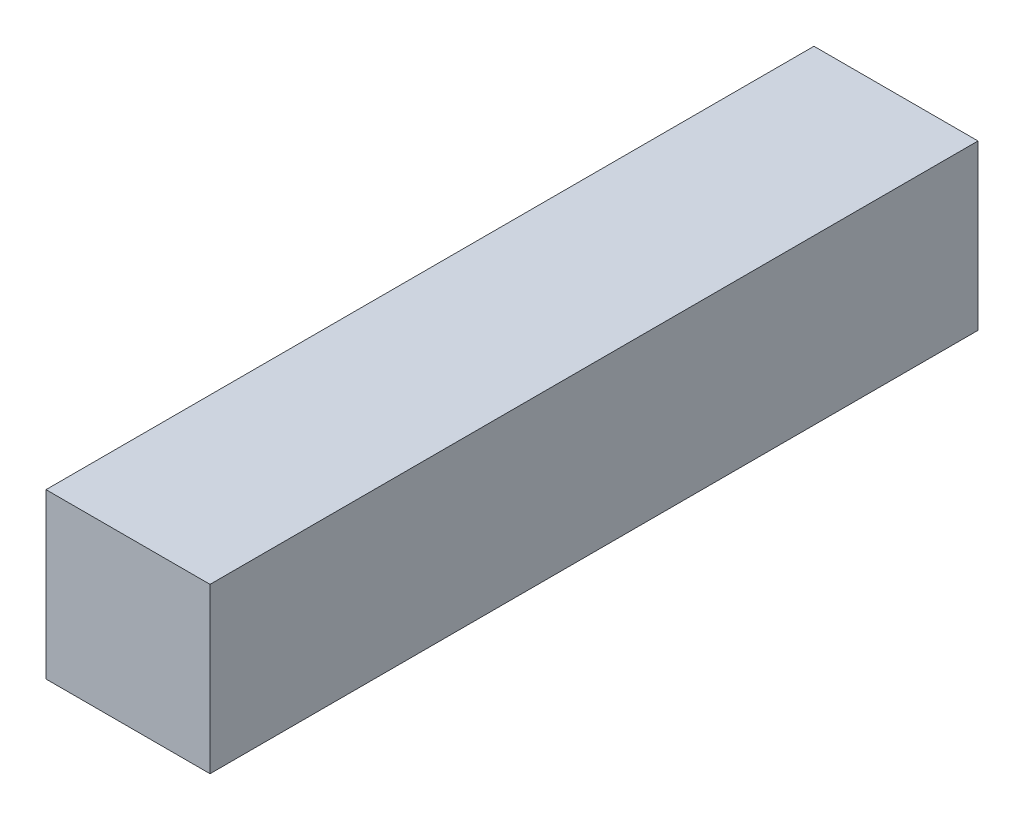
SolidWorks part; units mm, degrees
ref_plane "Face" through (0, 0, 0) normal (0, 0, 1) x (1, 0, 0)
ref_plane "Dessus" through (0, 0, 0) normal (0, 1, 0) x (1, 0, 0)
ref_plane "Droite" through (0, 0, 0) normal (1, 0, 0) x (0, 0, -1)
sketch "Esquisse1" plane through (0, 0, 0) normal (0, 0, 1) x (1, 0, 0)
  line L1 (0, 0) -> (22, 0)
  line L2 (0, 0) -> (0, 22)
  line L3 (0, 22) -> (22, 22)
  line L4 (22, 0) -> (22, 22)
  dimension "D1" = 22
  dimension "D2" = 22
extrude "Extrusion1" add sketch "Esquisse1" against normal blind 103
